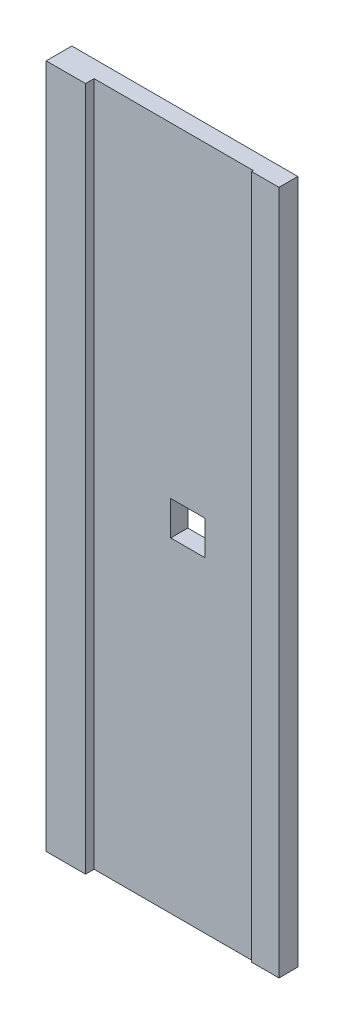
SolidWorks part; units mm, degrees
ref_plane "正面" through (0, 0, 0) normal (0, 0, 1) x (1, 0, 0)
ref_plane "平面" through (0, 0, 0) normal (0, 1, 0) x (1, 0, 0)
ref_plane "右側面" through (0, 0, 0) normal (1, 0, 0) x (0, 0, -1)
sketch "ｽｹｯﾁ1" plane through (0, 0, 0) normal (0, 0, 1) x (1, 0, 0)
  line L1 (0, 0) -> (132, 0)
  line L2 (0, 0) -> (0, 400)
  line L3 (0, 400) -> (132, 400)
  line L4 (132, 0) -> (132, 400)
  dimension "D1" = 132
  dimension "D2" = 400
extrude "ﾎﾞｽ - 押し出し1" add sketch "ｽｹｯﾁ1" along normal blind 10
sketch "ｽｹｯﾁ2" plane through (0, 0, 10) normal (0, 0, 1) x (1, 0, 0)
  line L0 (0, 0) -> (132, 0) construction
  line L1 (0, 400) -> (23, 400)
  line L2 (0, 400) -> (0, 0)
  line L3 (0, 0) -> (23, 0)
  line L4 (23, 400) -> (23, 0)
  dimension "D1" = 23
extrude "ﾎﾞｽ - 押し出し2" add sketch "ｽｹｯﾁ2" along normal blind 5
sketch "ｽｹｯﾁ3" plane through (0, 0, 10) normal (0, 0, 1) x (1, 0, 0)
  line L0 (23, 0) -> (132, 0) construction
  line L1 (132, 400) -> (116, 400)
  line L2 (132, 400) -> (132, 0)
  line L3 (132, 0) -> (116, 0)
  line L4 (116, 400) -> (116, 0)
  dimension "D1" = 16
extrude "ﾎﾞｽ - 押し出し3" add sketch "ｽｹｯﾁ3" along normal blind 1
sketch "ｽｹｯﾁ4" plane through (0, 0, 10) normal (0, 0, 1) x (1, 0, 0)
  line L0 (23, 200) -> (116, 200) construction
  line L1 (23, 0) -> (23, 400) construction
  line L2 (116, 400) -> (116, 0) construction
  line L3 (77.75, 400) -> (77.75, 0) construction
  line L4 (116, 400) -> (23, 400) construction
  line L5 (23, 0) -> (116, 0) construction
  line L7 (67.75, 190) -> (87.75, 190)
  line L8 (67.75, 190) -> (67.75, 210)
  line L9 (67.75, 210) -> (87.75, 210)
  line L10 (87.75, 190) -> (87.75, 210)
  line L11 (67.75, 190) -> (87.75, 210) construction
  line L12 (67.75, 210) -> (87.75, 190) construction
  point P12 (77.75, 200)
  dimension "D1" = 38.25
  dimension "D2" = 20
  dimension "D3" = 20
extrude "ｶｯﾄ - 押し出し1" cut sketch "ｽｹｯﾁ4" against normal through all
